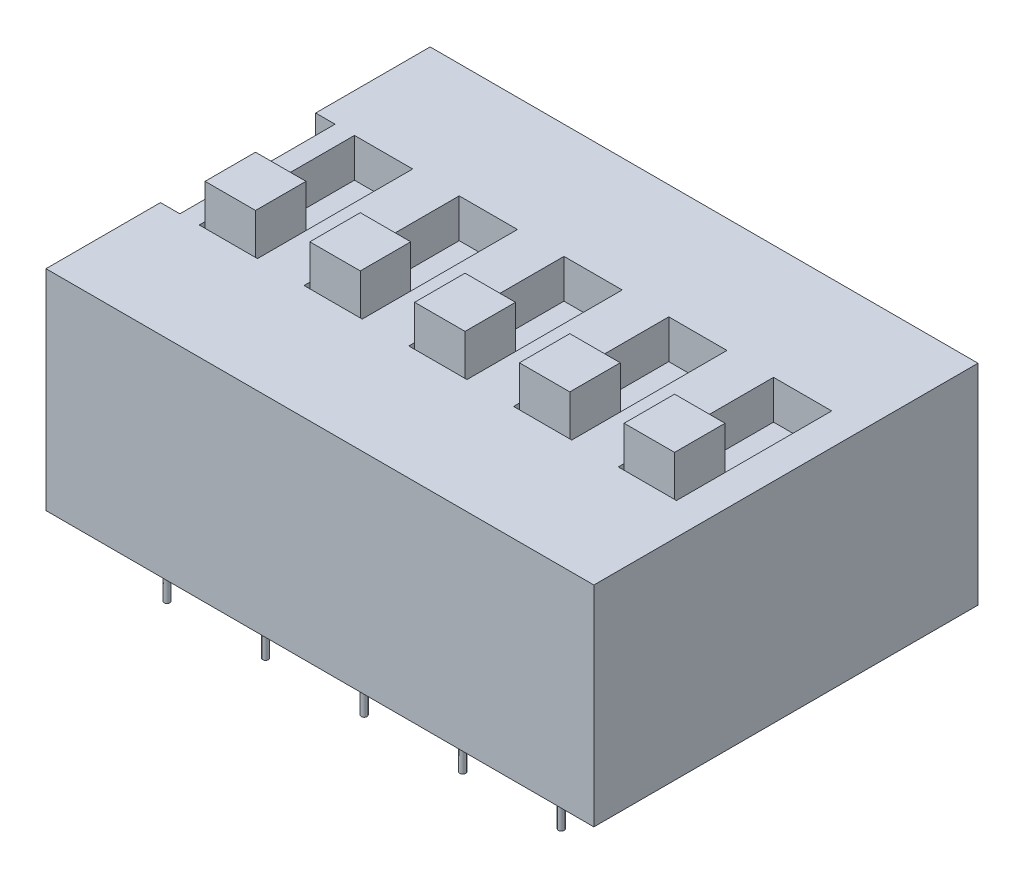
SolidWorks part; units mm, degrees
ref_plane "前视基准面" through (0, 0, 0) normal (0, 0, 1) x (1, 0, 0)
ref_plane "上视基准面" through (0, 0, 0) normal (0, 1, 0) x (1, 0, 0)
ref_plane "右视基准面" through (0, 0, 0) normal (1, 0, 0) x (0, 0, -1)
sketch "草图1" plane through (0, 0, 0) normal (0, 1, 0) x (1, 0, 0)
  line L1 (0, 0) -> (14.12, 0)
  line L2 (0, 0) -> (0, 9.9)
  line L3 (0, 9.9) -> (14.12, 9.9)
  line L4 (14.12, 0) -> (14.12, 9.9)
  dimension "D1" = 14.12
  dimension "D2" = 9.9
extrude "凸台-拉伸1" add sketch "草图1" along normal blind 5.4
sketch "草图2" plane through (0, 0, 0) normal (0, -1, 0) x (1, 0, 0)
  line L0 (0, -4.95) -> (14.12, -4.95) construction
  line L1 (0, -9.9) -> (0, 0) construction
  line L2 (14.12, 0) -> (14.12, -9.9) construction
  line L3 (7.06, -4.95) -> (7.06, 0) construction
  line L4 (0, 0) -> (14.12, 0) construction
  circle A0 centre (1.98, -1.14) radius 0.075
  circle A1 centre (4.52, -1.14) radius 0.075
  circle A2 centre (7.06, -1.14) radius 0.075
  circle A3 centre (9.6, -1.14) radius 0.075
  circle A4 centre (12.14, -1.14) radius 0.075
  circle A5 centre (4.52, -8.76) radius 0.075
  circle A6 centre (7.06, -8.76) radius 0.075
  circle A7 centre (9.6, -8.76) radius 0.075
  circle A8 centre (12.14, -8.76) radius 0.075
  circle A9 centre (1.98, -8.76) radius 0.075
  dimension "D1" = 0.15
  dimension "D2" = 5.08
  dimension "D3" = 3.81
  dimension "D4" = 5
  dimension "D5" = 2
extrude "凸台-拉伸2" add sketch "草图2" along normal blind 1.6
sketch "草图3" plane through (0, 5.4, 0) normal (0, 1, 0) x (1, 0, 0)
  line L0 (0, 9.9) -> (0, 0) construction
  line L1 (0, 6.95) -> (0.5, 6.95)
  line L2 (0, 6.95) -> (0, 2.95)
  line L3 (0, 2.95) -> (0.5, 2.95)
  line L4 (0.5, 6.95) -> (0.5, 2.95)
  point P6 (0, 4.95)
  dimension "D1" = 4
  dimension "D2" = 0.5
extrude "切除-拉伸1" cut sketch "草图3" against normal blind 4
sketch "草图4" plane through (0, 5.4, 0) normal (0, 1, 0) x (1, 0, 0)
  line L0 (0.5, 4.95) -> (14.12, 4.95) construction
  line L1 (0.5, 2.95) -> (0.5, 6.95) construction
  line L2 (14.12, 0) -> (14.12, 9.9) construction
  line L3 (3.7, 6.95) -> (3.7, 2.95)
  line L4 (1, 6.95) -> (2.5, 6.95)
  line L5 (1, 6.95) -> (1, 2.95)
  line L6 (1, 2.95) -> (2.5, 2.95)
  line L7 (2.5, 6.95) -> (2.5, 2.95)
  line L8 (1, 6.95) -> (2.5, 2.95) construction
  line L9 (1, 2.95) -> (2.5, 6.95) construction
  line L10 (3.7, 6.95) -> (5.2, 6.95)
  line L11 (5.2, 6.95) -> (5.2, 2.95)
  line L12 (3.7, 2.95) -> (5.2, 2.95)
  line L13 (6.4, 6.95) -> (6.4, 2.95)
  line L14 (6.4, 6.95) -> (7.9, 6.95)
  line L15 (7.9, 6.95) -> (7.9, 2.95)
  line L16 (6.4, 2.95) -> (7.9, 2.95)
  line L17 (9.1, 6.95) -> (9.1, 2.95)
  line L18 (9.1, 6.95) -> (10.6, 6.95)
  line L19 (10.6, 6.95) -> (10.6, 2.95)
  line L20 (9.1, 2.95) -> (10.6, 2.95)
  line L21 (11.8, 6.95) -> (11.8, 2.95)
  line L22 (11.8, 6.95) -> (13.3, 6.95)
  line L23 (13.3, 6.95) -> (13.3, 2.95)
  line L24 (11.8, 2.95) -> (13.3, 2.95)
  point P6 (1.75, 4.95)
  dimension "D1" = 1.5
  dimension "D2" = 4
  dimension "D4" = 0.5
  dimension "D3" = 5
extrude "切除-拉伸2" cut sketch "草图4" against normal blind 1
sketch "草图5" plane through (0, 4.4, 0) normal (0, 1, 0) x (1, 0, 0)
  line L0 (1.75, 2.95) -> (1.75, 6.95) construction
  line L1 (1, 2.95) -> (2.5, 2.95) construction
  line L2 (2.5, 6.95) -> (1, 6.95) construction
  line L3 (3.8, 4.3) -> (3.8, 3)
  line L4 (1.1, 4.3) -> (2.4, 4.3)
  line L5 (1.1, 4.3) -> (1.1, 3)
  line L6 (1.1, 3) -> (2.4, 3)
  line L7 (2.4, 4.3) -> (2.4, 3)
  line L8 (1.1, 4.3) -> (2.4, 3) construction
  line L9 (1.1, 3) -> (2.4, 4.3) construction
  line L10 (3.8, 4.3) -> (5.1, 4.3)
  line L11 (5.1, 4.3) -> (5.1, 3)
  line L12 (3.8, 3) -> (5.1, 3)
  line L13 (6.5, 4.3) -> (6.5, 3)
  line L14 (6.5, 4.3) -> (7.8, 4.3)
  line L15 (7.8, 4.3) -> (7.8, 3)
  line L16 (6.5, 3) -> (7.8, 3)
  line L17 (9.2, 4.3) -> (9.2, 3)
  line L18 (9.2, 4.3) -> (10.5, 4.3)
  line L19 (10.5, 4.3) -> (10.5, 3)
  line L20 (9.2, 3) -> (10.5, 3)
  line L21 (11.9, 4.3) -> (11.9, 3)
  line L22 (11.9, 4.3) -> (13.2, 4.3)
  line L23 (13.2, 4.3) -> (13.2, 3)
  line L24 (11.9, 3) -> (13.2, 3)
  point P6 (1.75, 3.65)
  dimension "D1" = 1.3
  dimension "D2" = 0.7
  dimension "D3" = 1.3
  dimension "D4" = 5
extrude "凸台-拉伸3" add sketch "草图5" along normal blind 2
